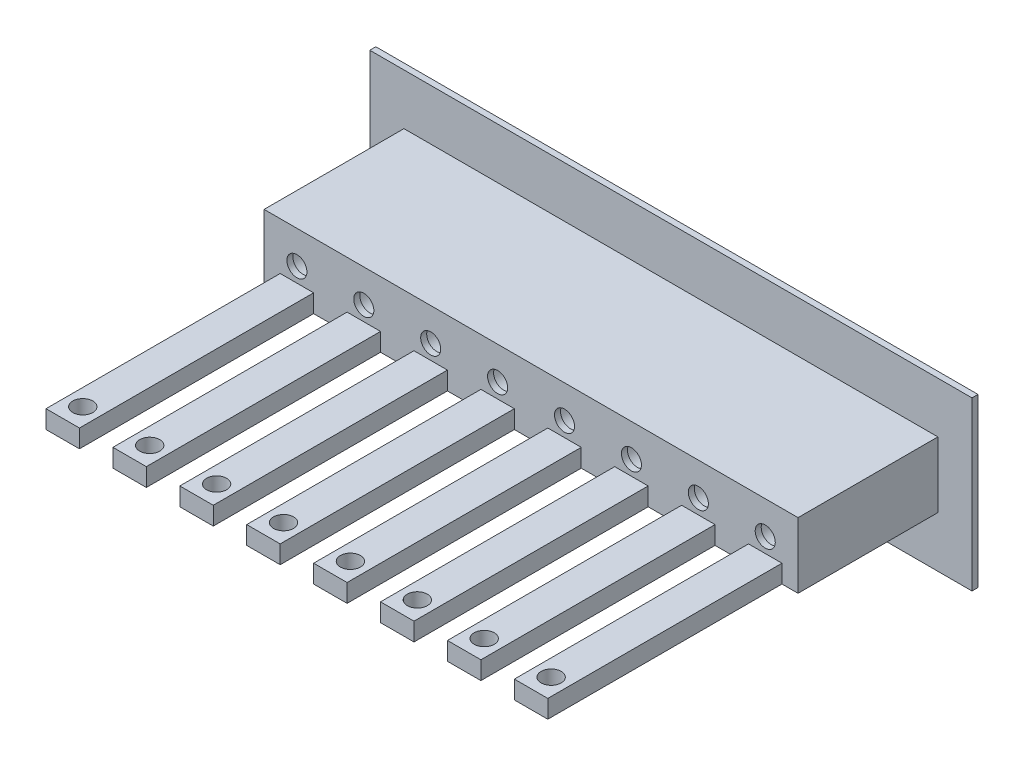
SolidWorks part; units mm, degrees
ref_plane "Alzado" through (0, 0, 0) normal (0, 0, 1) x (1, 0, 0)
ref_plane "Planta" through (0, 0, 0) normal (0, 1, 0) x (1, 0, 0)
ref_plane "Vista lateral" through (0, 0, 0) normal (1, 0, 0) x (0, 0, -1)
sketch "Croquis1" plane through (0, 0, 0) normal (0, 0, 1) x (1, 0, 0)
  line L1 (-92.4288, 22.3529) -> (-2.4288, 22.3529)
  line L2 (-92.4288, 22.3529) -> (-92.4288, -2.6471)
  line L3 (-92.4288, -2.6471) -> (-2.4288, -2.6471)
  line L4 (-2.4288, 22.3529) -> (-2.4288, -2.6471)
  dimension "D1" = 90
  dimension "D2" = 25
extrude "Saliente-Extruir1" add sketch "Croquis1" along normal blind 0.9
sketch "Croquis2" plane through (0, 0, 0.9) normal (0, 0, 1) x (1, 0, 0)
  line L1 (-92.4288, 22.3529) -> (-92.4288, -2.6471) construction
  line L2 (-2.4288, 22.3529) -> (-92.4288, 22.3529) construction
  circle A0 centre (-82.4288, 9.8529) radius 2.15
  circle A1 centre (-72.4288, 9.8529) radius 2.15
  circle A2 centre (-62.4288, 9.8529) radius 2.15
  circle A3 centre (-52.4288, 9.8529) radius 2.15
  circle A4 centre (-42.4288, 9.8529) radius 2.15
  circle A5 centre (-32.4288, 9.8529) radius 2.15
  circle A6 centre (-22.4288, 9.8529) radius 2.15
  circle A7 centre (-12.4288, 9.8529) radius 2.15
  dimension "D1" = 10
  dimension "D2" = 12.5
  dimension "D3" = 8
extrude "Cortar-Extruir1" cut sketch "Croquis2" against normal up to vertex (0.9 mm away)
sketch "Croquis3" plane through (0, 0, 0.9) normal (0, 0, 1) x (1, 0, 0)
  line L1 (-87.3288, 14.7529) -> (-7.5288, 14.7529)
  line L2 (-87.3288, 14.7529) -> (-87.3288, 4.9529)
  line L3 (-87.3288, 4.9529) -> (-7.5288, 4.9529)
  line L4 (-7.5288, 14.7529) -> (-7.5288, 4.9529)
  circle A0 centre (-12.4288, 9.8529) radius 2.15
  circle A1 centre (-22.4288, 9.8529) radius 2.15
  circle A2 centre (-32.4288, 9.8529) radius 2.15
  circle A3 centre (-42.4288, 9.8529) radius 2.15
  circle A4 centre (-52.4288, 9.8529) radius 2.15
  circle A5 centre (-62.4288, 9.8529) radius 2.15
  circle A6 centre (-72.4288, 9.8529) radius 2.15
  circle A7 centre (-82.4288, 9.8529) radius 2.15
extrude "Saliente-Extruir2" add sketch "Croquis3" along normal blind 20
sketch "Croquis4" plane through (0, 0, 20.9) normal (0, 0, 1) x (1, 0, 0)
  line L1 (-87.3288, 14.7529) -> (-7.5288, 14.7529)
  line L2 (-87.3288, 14.7529) -> (-87.3288, 4.9529)
  line L3 (-87.3288, 4.9529) -> (-7.5288, 4.9529)
  line L4 (-7.5288, 14.7529) -> (-7.5288, 4.9529)
  circle A0 centre (-82.4288, 9.8529) radius 1.5
  circle A1 centre (-72.4288, 9.8529) radius 1.5
  circle A2 centre (-62.4288, 9.8529) radius 1.5
  circle A3 centre (-52.4288, 9.8529) radius 1.5
  circle A4 centre (-42.4288, 9.8529) radius 1.5
  circle A5 centre (-32.4288, 9.8529) radius 1.5
  circle A6 centre (-22.4288, 9.8529) radius 1.5
  circle A7 centre (-12.4288, 9.8529) radius 1.5
  dimension "D1" = 8
extrude "Saliente-Extruir3" add sketch "Croquis4" along normal blind 0.9
sketch "Croquis5" plane through (0, 4.9529, 0) normal (0, -1, 0) x (1, 0, 0)
  line L0 (-87.3288, 21.8) -> (-84.9288, 21.8) construction
  line L1 (-87.3288, 21.8) -> (-7.5288, 21.8) construction
  line L2 (-84.9288, 21.8) -> (-79.9288, 21.8)
  line L3 (-79.9288, 21.8) -> (-79.9288, 56.8)
  line L4 (-79.9288, 56.8) -> (-84.9288, 56.8)
  line L5 (-84.9288, 56.8) -> (-84.9288, 21.8)
  line L6 (-74.9288, 21.8) -> (-69.9288, 21.8)
  line L7 (-69.9288, 21.8) -> (-69.9288, 56.8)
  line L8 (-69.9288, 56.8) -> (-74.9288, 56.8)
  line L9 (-74.9288, 56.8) -> (-74.9288, 21.8)
  line L10 (-77.3288, 21.8) -> (-74.9288, 21.8) construction
  line L11 (-64.9288, 21.8) -> (-59.9288, 21.8)
  line L12 (-59.9288, 21.8) -> (-59.9288, 56.8)
  line L13 (-59.9288, 56.8) -> (-64.9288, 56.8)
  line L14 (-64.9288, 56.8) -> (-64.9288, 21.8)
  line L15 (-67.3288, 21.8) -> (-64.9288, 21.8) construction
  line L16 (-54.9288, 21.8) -> (-49.9288, 21.8)
  line L17 (-49.9288, 21.8) -> (-49.9288, 56.8)
  line L18 (-49.9288, 56.8) -> (-54.9288, 56.8)
  line L19 (-54.9288, 56.8) -> (-54.9288, 21.8)
  line L20 (-57.3288, 21.8) -> (-54.9288, 21.8) construction
  line L21 (-44.9288, 21.8) -> (-39.9288, 21.8)
  line L22 (-39.9288, 21.8) -> (-39.9288, 56.8)
  line L23 (-39.9288, 56.8) -> (-44.9288, 56.8)
  line L24 (-44.9288, 56.8) -> (-44.9288, 21.8)
  line L25 (-47.3288, 21.8) -> (-44.9288, 21.8) construction
  line L26 (-34.9288, 21.8) -> (-29.9288, 21.8)
  line L27 (-29.9288, 21.8) -> (-29.9288, 56.8)
  line L28 (-29.9288, 56.8) -> (-34.9288, 56.8)
  line L29 (-34.9288, 56.8) -> (-34.9288, 21.8)
  line L30 (-37.3288, 21.8) -> (-34.9288, 21.8) construction
  line L31 (-24.9288, 21.8) -> (-19.9288, 21.8)
  line L32 (-19.9288, 21.8) -> (-19.9288, 56.8)
  line L33 (-19.9288, 56.8) -> (-24.9288, 56.8)
  line L34 (-24.9288, 56.8) -> (-24.9288, 21.8)
  line L35 (-27.3288, 21.8) -> (-24.9288, 21.8) construction
  line L36 (-14.9288, 21.8) -> (-9.9288, 21.8)
  line L37 (-9.9288, 21.8) -> (-9.9288, 56.8)
  line L38 (-9.9288, 56.8) -> (-14.9288, 56.8)
  line L39 (-14.9288, 56.8) -> (-14.9288, 21.8)
  line L40 (-17.3288, 21.8) -> (-14.9288, 21.8) construction
  circle A0 centre (-82.4288, 53.8) radius 1.5
  circle A1 centre (-72.4288, 53.8) radius 1.5
  circle A2 centre (-62.4288, 53.8) radius 1.5
  circle A3 centre (-52.4288, 53.8) radius 1.5
  circle A4 centre (-42.4288, 53.8) radius 1.5
  circle A5 centre (-32.4288, 53.8) radius 1.5
  circle A6 centre (-22.4288, 53.8) radius 1.5
  circle A7 centre (-12.4288, 53.8) radius 1.5
  dimension "D1" = 3
  dimension "D2" = 8
extrude "Saliente-Extruir4" add sketch "Croquis5" against normal blind 2.7
